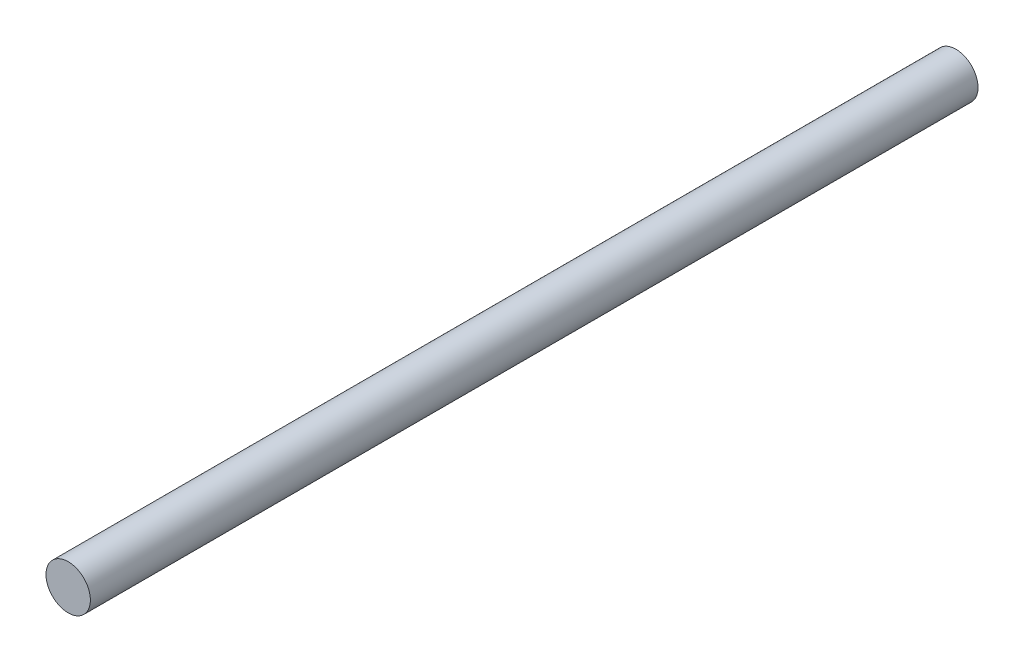
SolidWorks part; units mm, degrees
material "Custom Plastic"
ref_plane "Front Plane" through (0, 0, 0) normal (0, 0, 1) x (1, 0, 0)
ref_plane "Top Plane" through (0, 0, 0) normal (0, 1, 0) x (1, 0, 0)
ref_plane "Right Plane" through (0, 0, 0) normal (1, 0, 0) x (0, 0, -1)
ref_plane "Plane1" through (0, 0, 0) normal (0, -1, 0) x (1, 0, 0)
sketch "Sketch1" plane through (0, 0, 0) normal (0, -1, 0) x (1, 0, 0)
  line L0 (1.5875, 63.5) -> (0, 63.5)
  line L1 (0, 63.5) -> (0, 0)
  line L2 (0, 0) -> (1.5875, 0)
  line L3 (1.5875, 0) -> (1.5875, 63.5)
  line L4 (0, 63.5) -> (0, 0) construction
revolve "Revolve1" add sketch "Sketch1" angle 360 about L4
